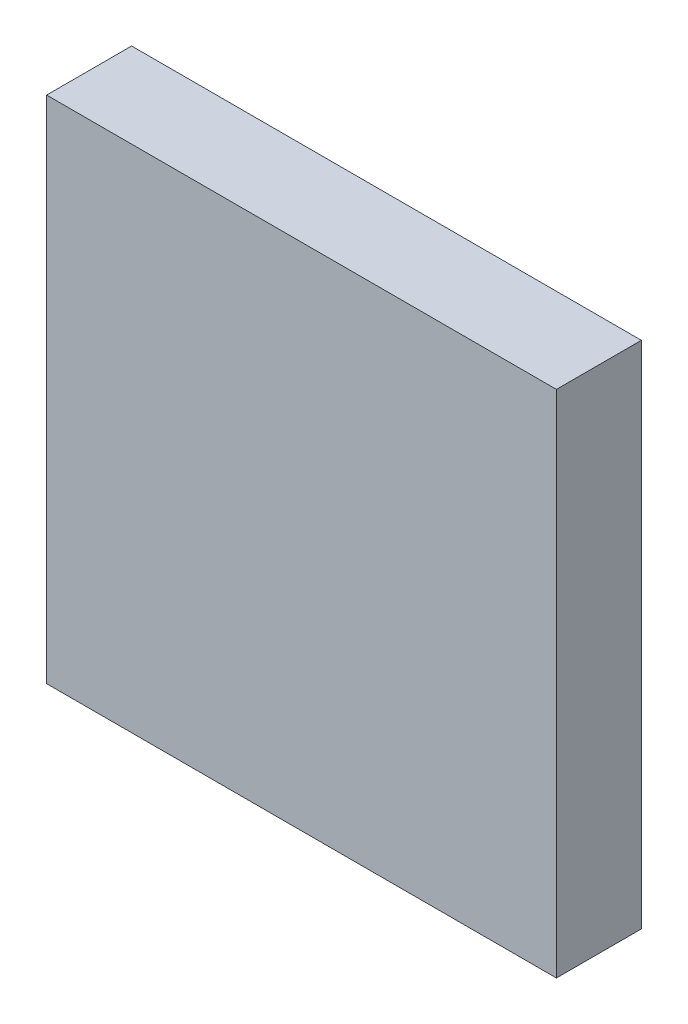
SolidWorks part; units mm, degrees
ref_plane "Alzado" through (0, 0, 0) normal (0, 0, 1) x (1, 0, 0)
ref_plane "Planta" through (0, 0, 0) normal (0, 1, 0) x (1, 0, 0)
ref_plane "Vista lateral" through (0, 0, 0) normal (1, 0, 0) x (0, 0, -1)
sketch "Croquis1" plane through (0, 0, 0) normal (0, 0, 1) x (1, 0, 0)
  line L1 (-30, 30) -> (30, 30)
  line L2 (-30, 30) -> (-30, -30)
  line L3 (-30, -30) -> (30, -30)
  line L4 (30, 30) -> (30, -30)
  line L5 (-30, 30) -> (30, -30) construction
  line L6 (-30, -30) -> (30, 30) construction
  point P0 (0, 0)
extrude "Saliente-Extruir1" add sketch "Croquis1" along normal blind 10
